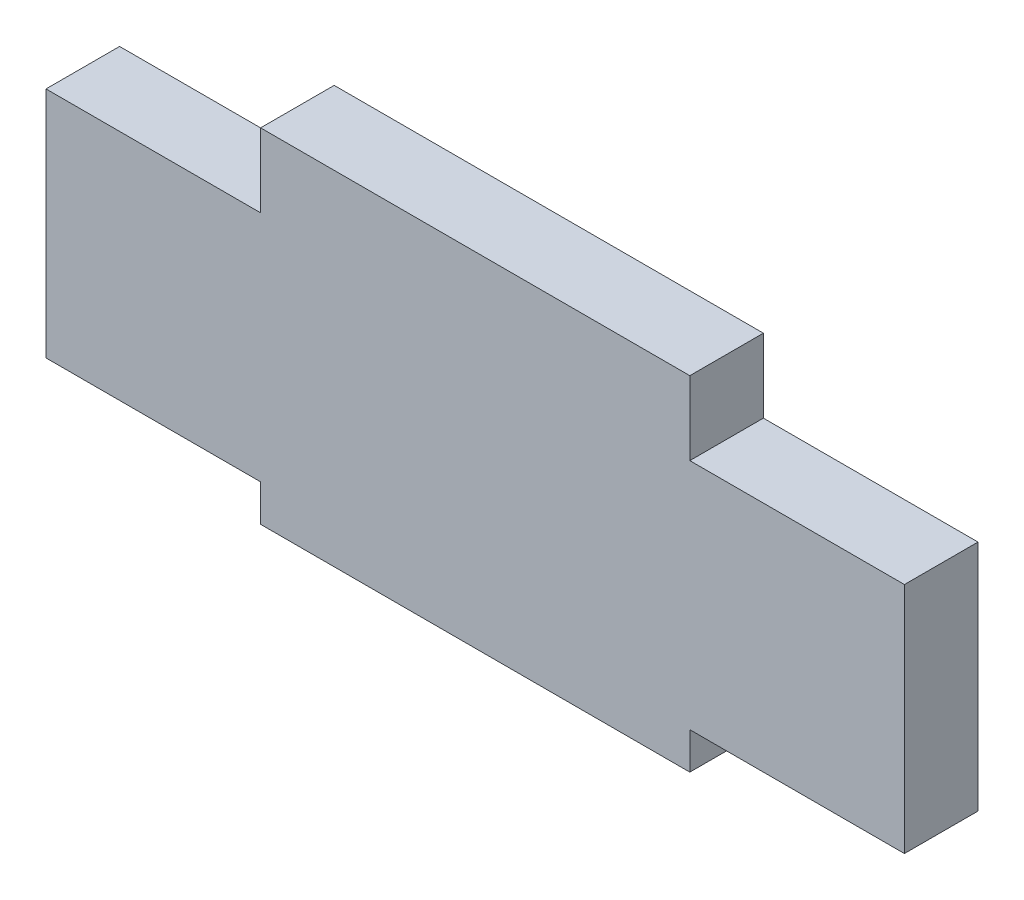
SolidWorks part; units mm, degrees
material "Acrílico (médio-alto impacto)"
ref_plane "Plano frontal" through (0, 0, 0) normal (0, 0, 1) x (1, 0, 0)
ref_plane "Plano superior" through (0, 0, 0) normal (0, 1, 0) x (1, 0, 0)
ref_plane "Plano direito" through (0, 0, 0) normal (1, 0, 0) x (0, 0, -1)
sketch "Esboço1" plane through (0, 0, 0) normal (0, 0, 1) x (1, 0, 0)
  line L0 (0, 0) -> (35, 0) construction
  line L1 (-35, -9.5) -> (35, -9.5)
  line L2 (-35, -9.5) -> (-35, 9.5)
  line L3 (-35, 9.5) -> (35, 9.5)
  line L4 (35, -9.5) -> (35, 9.5)
  line L5 (-35, -9.5) -> (35, 9.5) construction
  line L6 (-35, 9.5) -> (35, -9.5) construction
  line L7 (17.5, 15.5) -> (-17.5, 15.5)
  line L8 (17.5, 15.5) -> (17.5, 9.5)
  line L9 (17.5, 9.5) -> (-17.5, 9.5)
  line L10 (-17.5, 15.5) -> (-17.5, 9.5)
  line L11 (17.5, 15.5) -> (-17.5, 9.5) construction
  line L12 (17.5, 9.5) -> (-17.5, 15.5) construction
  line L13 (17.5, -9.5) -> (-17.5, -9.5)
  line L17 (-17.5, -9.5) -> (-17.5, -12.5)
  line L18 (-17.5, -12.5) -> (17.5, -12.5)
  line L19 (17.5, -12.5) -> (17.5, -9.5)
  point P0 (0, 0)
  point P6 (0, 12.5)
  dimension "D1" = 6
  dimension "D2" = 35
  dimension "D3" = 19
  dimension "D4" = 70
  dimension "D5" = 3
extrude "Ressalto-extrusão1" add sketch "Esboço1" along normal blind 6
